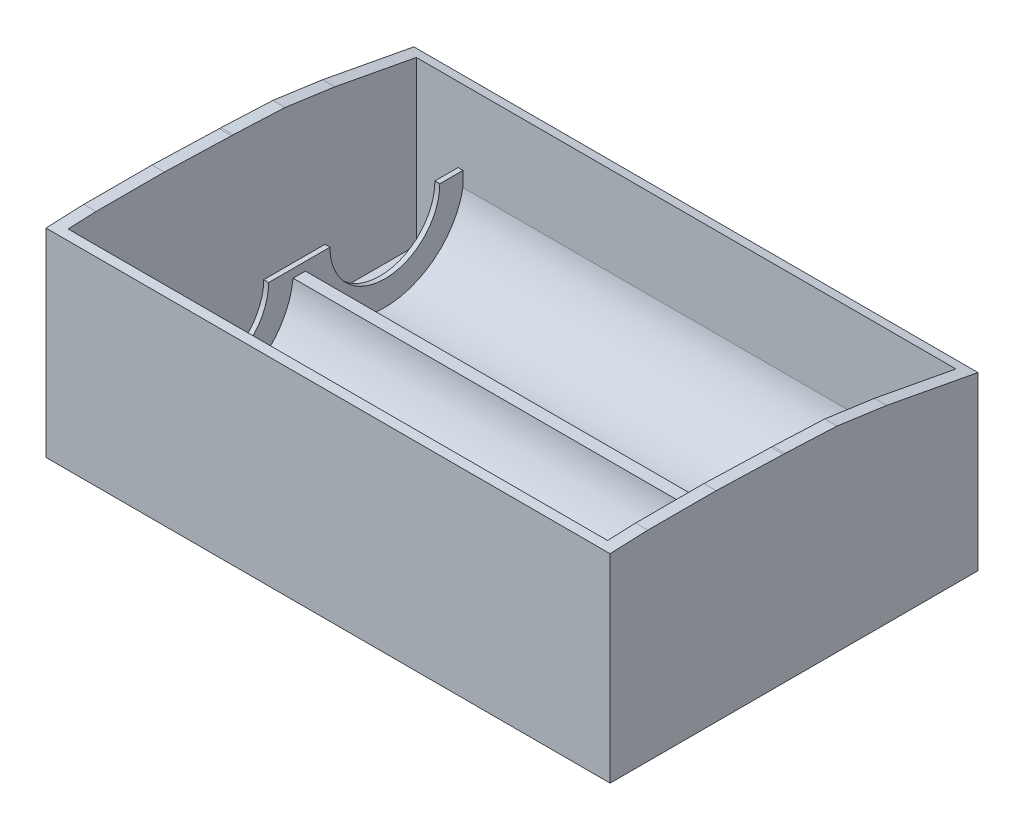
SolidWorks part; units mm, degrees
ref_plane "Front Plane" through (0, 0, 0) normal (0, 0, 1) x (1, 0, 0)
ref_plane "Top Plane" through (0, 0, 0) normal (0, 1, 0) x (1, 0, 0)
ref_plane "Right Plane" through (0, 0, 0) normal (1, 0, 0) x (0, 0, -1)
sketch "Sketch16" plane through (0, 0, 0) normal (1, 0, 0) x (0, 0, -1)
  line L0 (21.5465, 40.6394) -> (7.6186, 40.6394)
  line L1 (21.5465, 40.6394) -> (35.2383, 40.2055)
  line L2 (35.2383, 40.2055) -> (35.6026, 40.2055)
  line L3 (35.6026, 40.2055) -> (46.1712, 39.7312)
  line L4 (46.1712, 39.7312) -> (56.2876, 38.3122)
  line L5 (56.2876, 38.3122) -> (74.9264, 34.8087)
  line L6 (74.9264, 34.8087) -> (74.9264, -0.1913)
  line L7 (-0.0736, -0.1913) -> (74.9264, -0.1913)
  line L8 (-0.0736, -0.1913) -> (-0.0736, 40.3184)
  line L9 (-0.0736, 40.3184) -> (7.6186, 40.6394)
  dimension "D1" = 75
  dimension "D2" = 35
extrude "Boss-Extrude6" add sketch "Sketch16" along normal blind 115
sketch "Sketch17" plane through (0, 0, 0) normal (0, 1, 0) x (1, 0, 0)
  line L0 (0, 74.9264) -> (0, 56.2876) construction
  line L1 (2.5, 72.9264) -> (112.5, 72.9264)
  line L2 (2.5, 72.9264) -> (2.5, 1.9264)
  line L3 (2.5, 1.9264) -> (112.5, 1.9264)
  line L4 (112.5, 72.9264) -> (112.5, 1.9264)
  line L8 (115, 74.9264) -> (0, 74.9264) construction
  dimension "D1" = 110
  dimension "D2" = 2.5
  dimension "D3" = 71
  dimension "D4" = 2
extrude "Cut-Extrude5" cut sketch "Sketch17" along normal blind 115 from offset 2
sketch "Sketch18" plane through (0, 2, 0) normal (0, 1, 0) x (1, 0, 0)
  line L0 (0, 56.2876) -> (0, 46.1712) construction
  line L1 (12, 71.4264) -> (103, 71.4264)
  line L2 (12, 71.4264) -> (12, 3.4264)
  line L3 (12, 3.4264) -> (103, 3.4264)
  line L4 (103, 71.4264) -> (103, 3.4264)
  line L5 (112.5, 72.9264) -> (2.5, 72.9264) construction
  dimension "D1" = 91
  dimension "D2" = 12
  dimension "D3" = 68
  dimension "D4" = 1.5
sketch "Sketch21" plane through (0, 0, 0) normal (-1, 0, 0) x (0, 0, 1)
  line L0 (-73.213, 2) -> (-73.213, 20)
  line L1 (-5.8972, 2) -> (-5.8972, 20)
  line L2 (-40.8051, 18.2725) -> (-38.3051, 18.2725)
  line L3 (-71.4264, 2) -> (-3.4264, 2) construction
  line L4 (-73.213, 2) -> (-5.8972, 2)
  arc A0 (-73.213, 20) -> (-40.8051, 18.2725) centre (-56.963, 20) ccw
  arc A1 (-5.8972, 20) -> (-38.3051, 18.2725) centre (-22.1472, 20) cw
  dimension "D2" = 16.25
  dimension "D3" = 16.25
  dimension "D4" = 18
  dimension "D1" = 2.5
  dimension "D5" = 18
extrude "Boss-Extrude7" add sketch "Sketch21" against normal up to vertex (103 mm away) from vertex at -12 starting at point (12, 2, -71.4264)
sketch "Sketch22" plane through (0, 2, 0) normal (0, 1, 0) x (1, 0, 0)
  line L0 (12, 5.8972) -> (12, 1.9264)
  line L1 (2.5, 1.9264) -> (112.5, 1.9264) construction
  line L2 (12, 1.9264) -> (103, 1.9264)
  line L3 (2.5, 1.9264) -> (112.5, 1.9264) construction
  line L4 (103, 1.9264) -> (103, 5.8972)
  line L5 (103, 5.8972) -> (12, 5.8972)
  line L7 (12, 72.9264) -> (2.5, 72.9264) construction
  line L8 (2.5, 72.9264) -> (2.5, 1.9264) construction
  line L9 (112.5, 1.9264) -> (112.5, 7.6186) construction
  circle A0 centre (7, 69.4264) radius 3
  circle A1 centre (108, 69.4264) radius 3
  circle A2 centre (108, 5.4264) radius 3
  circle A3 centre (7, 5.4264) radius 3
  dimension "D5" = 6
  dimension "D1" = 3.5
  dimension "D2" = 3.5
  dimension "D3" = 4.5
  dimension "D4" = 4.5
extrude "Cut-Extrude6" cut sketch "Sketch22" against normal through all
sketch "Sketch23" plane through (0, 0, 0) normal (-1, 0, 0) x (0, 0, 1)
  line L0 (-73.213, 20) -> (-5.8972, 20)
  line L1 (-5.8972, 20) -> (-5.8972, 2)
  line L2 (-5.8972, 2) -> (-73.213, 2)
  line L3 (-73.213, 2) -> (-73.213, 20)
extrude "Boss-Extrude8" add sketch "Sketch23" along normal blind 1 from surface at -12 starting at face at (12, 8.0483, -39.2288)
sketch "Sketch24" plane through (115, 0, 0) normal (1, 0, 0) x (0, 0, -1)
  line L0 (5.8972, 20) -> (73.213, 20)
  line L1 (73.213, 20) -> (73.213, 2)
  line L2 (73.213, 2) -> (5.8972, 2)
  line L3 (5.8972, 2) -> (5.8972, 20)
extrude "Boss-Extrude9" add sketch "Sketch24" along normal blind 1 from surface at -12 starting at face at (103, 8.0483, -39.2288)
sketch "Sketch25" plane through (11, 0, 0) normal (-1, 0, 0) x (0, 0, 1)
  line L6 (-68.2051, 20) -> (-45.8051, 20)
  line L7 (-33.3051, 20) -> (-10.9051, 20)
  arc A0 (-68.2051, 20) -> (-45.8051, 20) centre (-57.0051, 20) ccw
  arc A1 (-33.3051, 20) -> (-10.9051, 20) centre (-22.1051, 20) ccw
  dimension "D1" = 11.2
  dimension "D2" = 11.2
  dimension "D3" = 5
  dimension "D4" = 5
extrude "Cut-Extrude7" cut sketch "Sketch25" against normal up to surface (1 mm away) up to face at (12, 12.858, -45.8952)
sketch "Sketch26" plane through (104, 0, 0) normal (1, 0, 0) x (0, 0, -1)
  line L10 (10.9051, 20) -> (33.3051, 20)
  line L11 (45.8051, 20) -> (68.2051, 20)
  arc A2 (10.9051, 20) -> (33.3051, 20) centre (22.1051, 20) ccw
  arc A3 (45.8051, 20) -> (68.2051, 20) centre (57.0051, 20) ccw
  dimension "D1" = 11.2
  dimension "D4" = 11.2
extrude "Cut-Extrude8" cut sketch "Sketch26" against normal up to surface (1 mm away) up to face at (103, 12.858, -45.8952)
